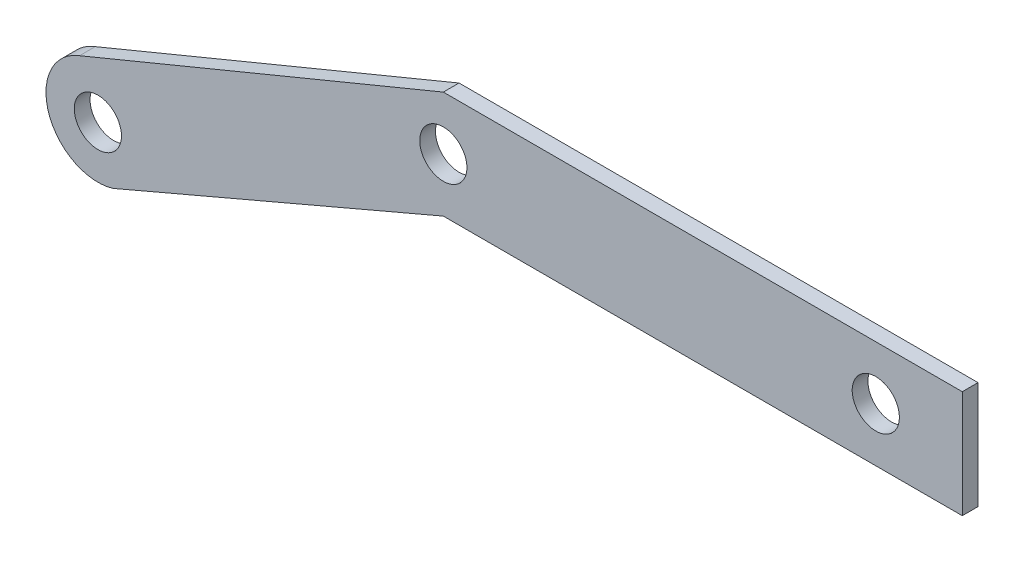
SolidWorks part; units mm, degrees
ref_plane "Alzado" through (0, 0, 0) normal (0, 0, 1) x (1, 0, 0)
ref_plane "Planta" through (0, 0, 0) normal (0, 1, 0) x (1, 0, 0)
ref_plane "Vista lateral" through (0, 0, 0) normal (1, 0, 0) x (0, 0, -1)
sketch "Model" plane through (0, 0, 0) normal (0, 0, 1) x (1, 0, 0)
  line L0 (6.2612, 18.7694) -> (-14.7395, 9.795)
  line L1 (-16.8722, 16.0373) -> (6.2612, 25.6004)
  line L2 (6.2612, 25.6004) -> (39.2612, 25.6004)
  line L3 (6.2612, 18.7694) -> (39.2612, 18.7694)
  line L4 (39.2612, 25.6004) -> (39.2612, 18.7694)
  arc A1 (-16.8722, 16.0373) -> (-14.7395, 9.795) centre (-15.7058, 12.9504) ccw
  circle A20 centre (33.7612, 22.1849) radius 1.5
  circle A21 centre (6.2612, 22.1849) radius 1.5
  circle A22 centre (-15.7058, 12.9504) radius 1.5
  dimension "D1" = 33
extrude "Saliente-Extruir1" add sketch "Model" along normal blind 1
